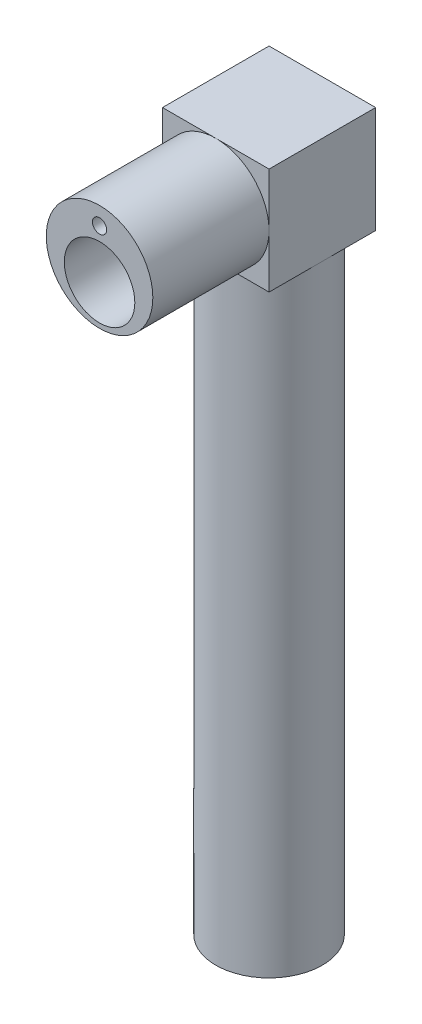
SolidWorks part; units mm, degrees
ref_plane "Front Plane" through (0, 0, 0) normal (0, 0, 1) x (1, 0, 0)
ref_plane "Top Plane" through (0, 0, 0) normal (0, 1, 0) x (1, 0, 0)
ref_plane "Right Plane" through (0, 0, 0) normal (1, 0, 0) x (0, 0, -1)
sketch "Sketch1" plane through (0, 0, 0) normal (0, 0, 1) x (1, 0, 0)
  circle A0 centre (0, 0) radius 28.1
extrude "Boss-Extrude2" add sketch "Sketch1" along normal blind 61.3
sketch "Sketch3" plane through (0, 0, 61.3) normal (0, 0, 1) x (1, 0, 0)
  circle A1 centre (0, -7) radius 18.6
extrude "Cut-Extrude2" cut sketch "Sketch3" against normal blind 58.8 contours A1
sketch "Sketch4" plane through (0, 0, 0) normal (0, 0, -1) x (-1, 0, 0)
  line L1 (-28.1, -28.1) -> (28.1, -28.1)
  line L2 (-28.1, -28.1) -> (-28.1, 28.1)
  line L3 (-28.1, 28.1) -> (28.1, 28.1)
  line L4 (28.1, -28.1) -> (28.1, 28.1)
  line L5 (-28.1, -28.1) -> (28.1, 28.1) construction
  line L6 (-28.1, 28.1) -> (28.1, -28.1) construction
  point P0 (0, 0)
extrude "Boss-Extrude3" add sketch "Sketch4" along normal blind 56.2
sketch "Sketch5" plane through (0, 0, 2.5) normal (0, 0, 1) x (1, 0, 0)
  circle A1 centre (0, -7) radius 16.1
extrude "Cut-Extrude4" cut sketch "Sketch5" against normal blind 5
sketch "Sketch6" plane through (0, 0, -56.2) normal (0, 0, -1) x (-1, 0, 0)
  line L1 (-24.8987, -24.8896) -> (24.8987, -24.8896)
  line L2 (-24.8987, -24.8896) -> (-24.8987, 24.8896)
  line L3 (-24.8987, 24.8896) -> (24.8987, 24.8896)
  line L4 (24.8987, -24.8896) -> (24.8987, 24.8896)
  line L5 (-24.8987, -24.8896) -> (24.8987, 24.8896) construction
  line L6 (-24.8987, 24.8896) -> (24.8987, -24.8896) construction
  point P0 (0, 0)
extrude "Cut-Extrude5" cut sketch "Sketch6" against normal blind 53.7
sketch "Sketch7" plane through (0, -28.1, 0) normal (0, -1, 0) x (-1, 0, 0)
  circle A0 centre (0, 28.1) radius 28.1
extrude "Boss-Extrude4" add sketch "Sketch7" along normal blind 321.5 contours A0
sketch "Sketch8" plane through (0, -349.6, 0) normal (0, -1, 0) x (-1, 0, 0)
  line L1 (-1.6583, 25.8321) -> (1.6583, 25.8321)
  line L3 (-1.6583, 30.8321) -> (1.6583, 30.8321)
  arc A2 (-1.6583, 30.8321) -> (-1.6583, 25.8321) centre (0, 28.3321) ccw
  arc A3 (1.6583, 25.8321) -> (1.6583, 30.8321) centre (0, 28.3321) ccw
extrude "Cut-Extrude6" cut sketch "Sketch8" against normal blind 10
sketch "Sketch9" plane through (0, -349.6, 0) normal (0, -1, 0) x (-1, 0, 0)
  circle A1 centre (0, 28.3321) radius 3
extrude "Cut-Extrude7" cut sketch "Sketch9" against normal blind 1
sketch "Sketch10" plane through (0, -349.6, 0) normal (0, -1, 0) x (-1, 0, 0)
  circle A1 centre (0, 28.3321) radius 6.025
extrude "Cut-Extrude8" cut sketch "Sketch10" against normal blind 0.1
sketch "Sketch15" plane through (0, -349.6, 0) normal (0, -1, 0) x (-1, 0, 0)
  line L0 (6.025, 28.3321) -> (-6.025, 28.3321)
  circle A0 centre (0, 28.3321) radius 6.025 construction
  arc A1 (15, 28.3321) -> (-15, 28.3321) centre (0, 28.3321) ccw
sketch3d "3DSketch2"
  line L1 (-15, -349.6, -28.3321) -> (-22.5, -349.6, -28.3321)
  line L2 (-15, -349.6, -28.3321) -> (-15, -20, -28.3321)
  line L3 (-15, -20, -28.3321) -> (-22.5, -20, -28.3321)
  line L4 (-22.5, -349.6, -28.3321) -> (-22.5, -20, -28.3321)
sweep "Cut-Sweep4" cut profiles "3DSketch2" path "Sketch15"
sketch "Sketch18" plane through (0, 0, 61.3) normal (0, 0, 1) x (1, 0, 0)
  circle A1 centre (0, 18.75) radius 3.75
extrude "Cut-Extrude9" cut sketch "Sketch18" against normal blind 100
sketch "Sketch19" plane through (0, -349.6, 0) normal (0, -1, 0) x (-1, 0, 0)
  circle A0 centre (-18.75, 28.3321) radius 3.75
  circle A1 centre (18.75, 28.3321) radius 3.75
extrude "Cut-Extrude11" cut sketch "Sketch19" against normal blind 325
